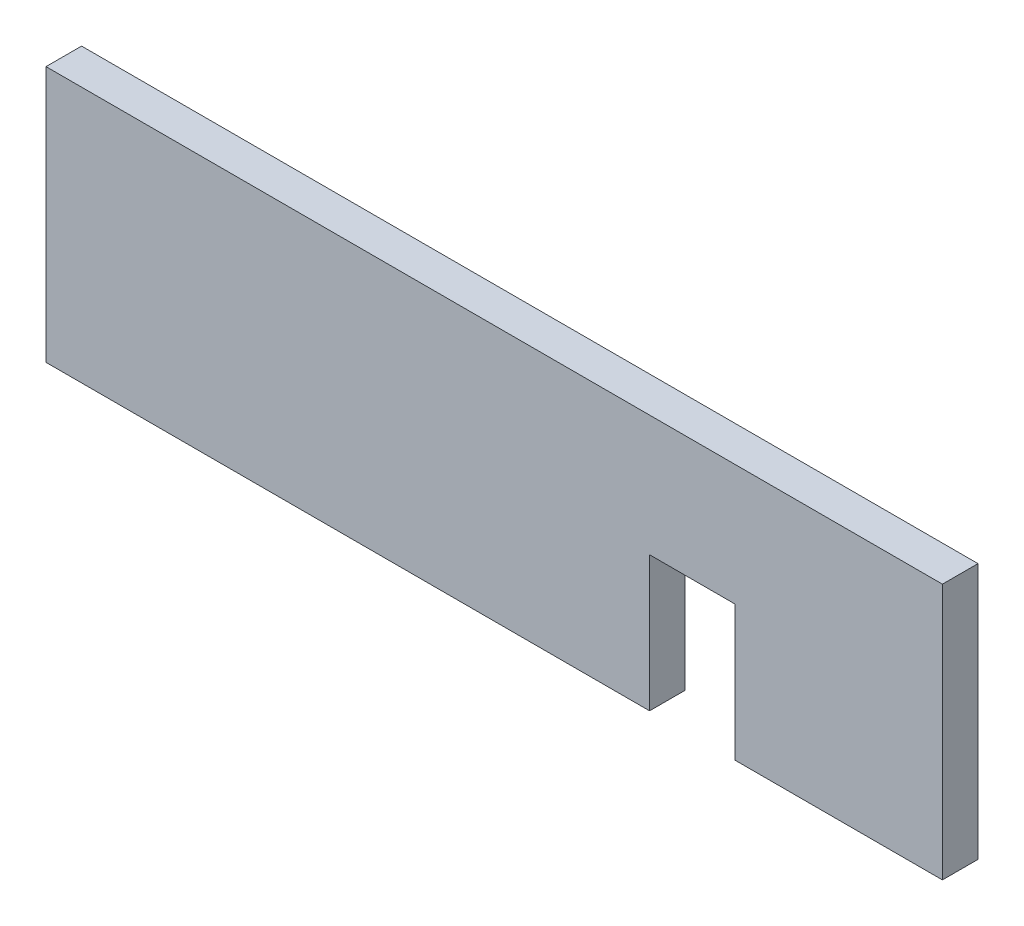
SolidWorks part; units mm, degrees
ref_plane "Front Plane" through (0, 0, 0) normal (0, 0, 1) x (1, 0, 0)
ref_plane "Top Plane" through (0, 0, 0) normal (0, 1, 0) x (1, 0, 0)
ref_plane "Right Plane" through (0, 0, 0) normal (1, 0, 0) x (0, 0, -1)
sketch "Sketch1" plane through (0, 0, 0) normal (0, 0, 1) x (1, 0, 0)
  line L1 (-64.8627, 12.0429) -> (-24.8627, 12.0429)
  line L2 (-64.8627, 12.0429) -> (-64.8627, 0.6129)
  line L3 (-64.8627, 0.6129) -> (-24.8627, 0.6129)
  line L4 (-24.8627, 12.0429) -> (-24.8627, 0.6129)
  dimension "D1" = 40
  dimension "D2" = 11.43
extrude "Boss-Extrude1" add sketch "Sketch1" along normal blind 1.5875
sketch "Sketch2" plane through (0, 0, 1.5875) normal (0, 0, 1) x (1, 0, 0)
  line L0 (-24.8627, 0.6129) -> (-24.8627, 12.0429) construction
  line L1 (-34.1209, 6.6462) -> (-37.9309, 6.6462)
  line L2 (-34.1209, 6.6462) -> (-34.1209, 0.3404)
  line L3 (-34.1209, 0.3404) -> (-37.9309, 0.3404)
  line L4 (-37.9309, 6.6462) -> (-37.9309, 0.3404)
  dimension "D1" = 3.81
  dimension "D2" = 6.3057
  dimension "D3" = 9.2582
extrude "Cut-Extrude1" cut sketch "Sketch2" against normal blind 2.54
